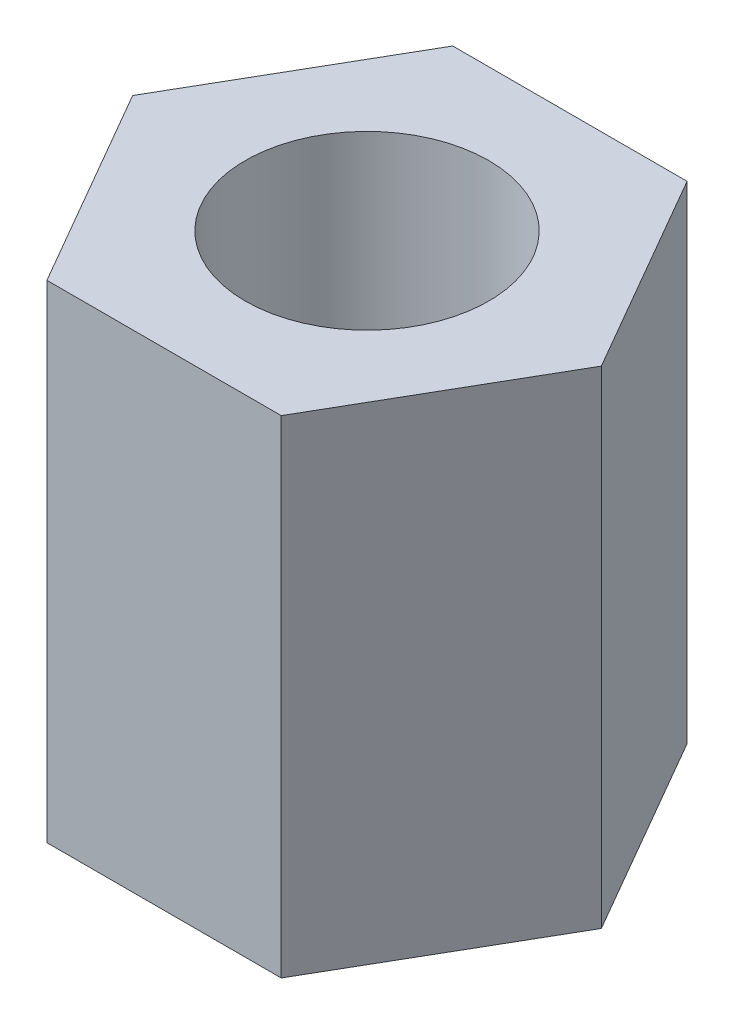
SolidWorks part; units mm, degrees
material "ABS"
ref_plane "Alzado" through (0, 0, 0) normal (0, 0, 1) x (1, 0, 0)
ref_plane "Planta" through (0, 0, 0) normal (0, 1, 0) x (1, 0, 0)
ref_plane "Vista lateral" through (0, 0, 0) normal (1, 0, 0) x (0, 0, -1)
sketch "Croquis1" plane through (0, 0, 0) normal (0, 1, 0) x (1, 0, 0)
  line L1 (1.4434, -2.5) -> (2.8868, 0)
  line L2 (2.8868, 0) -> (1.4434, 2.5)
  line L3 (1.4434, 2.5) -> (-1.4434, 2.5)
  line L4 (-1.4434, 2.5) -> (-2.8868, 0)
  line L5 (-2.8868, 0) -> (-1.4434, -2.5)
  line L6 (-1.4434, -2.5) -> (1.4434, -2.5)
  circle A0 centre (0, 0) radius 2.5 construction
  circle A1 centre (0, 0) radius 1.5
  dimension "D2" = 3
  dimension "D1" = 5
extrude "Saliente-Extruir1" add sketch "Croquis1" along normal mid plane 6
